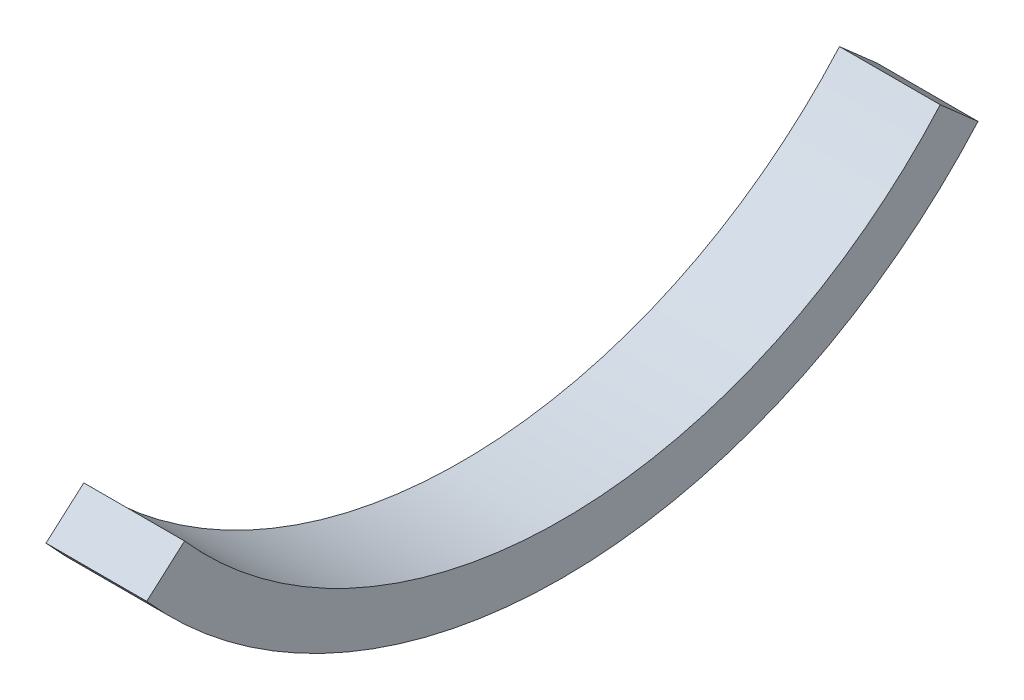
SolidWorks part; units mm, degrees
ref_plane "Front Plane" through (0, 0, 0) normal (0, 0, 1) x (1, 0, 0)
ref_plane "Top Plane" through (0, 0, 0) normal (0, 1, 0) x (1, 0, 0)
ref_plane "Right Plane" through (0, 0, 0) normal (1, 0, 0) x (0, 0, -1)
sketch "Sketch1" plane through (0, 0, 0) normal (1, 0, 0) x (0, 0, -1)
  line L0 (19.05, -16.8005) -> (-19.05, -16.8005) construction
  line L1 (20.955, -18.4806) -> (19.05, -16.8005)
  line L2 (-19.05, -16.8005) -> (-20.955, -18.4806)
  arc A2 (19.05, -16.8005) -> (-19.05, -16.8005) centre (0, 0) cw
  arc A3 (20.955, -18.4806) -> (-20.955, -18.4806) centre (0, 0) cw
  point P8 (0, 0)
  dimension "D1" = 2.54
  dimension "D2" = 25.4
  dimension "D3" = 38.1
extrude "Boss-Extrude1" add sketch "Sketch1" along normal blind 5.08
equation "\"TubeR\"= 0.8in"
equation "\"Foamcore\"= 0.2in"
equation "\"MDF\"= 0.2in"
equation "\"NutD\"= 0.2145in"
equation "\"NutH\"= 0.0915in"
equation "\"MountScrewL\"= 0.3in"
equation "\"MountScrewD\"= 3.6mm"
equation "\"D1@Boss-Extrude1\"=\"Foamcore\""
